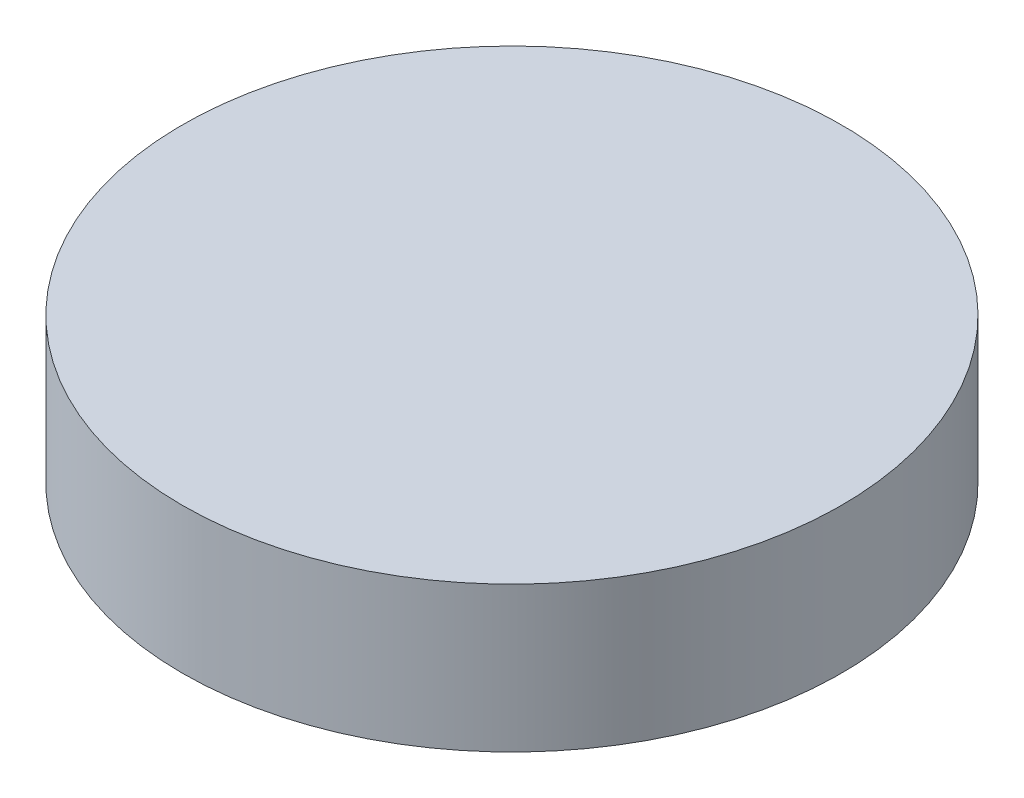
SolidWorks part; units mm, degrees
ref_plane "Front Plane" through (0, 0, 0) normal (0, 0, 1) x (1, 0, 0)
ref_plane "Top Plane" through (0, 0, 0) normal (0, 1, 0) x (1, 0, 0)
ref_plane "Right Plane" through (0, 0, 0) normal (1, 0, 0) x (0, 0, -1)
sketch "Sketch1" plane through (0, 0, 0) normal (0, 1, 0) x (1, 0, 0)
  circle A0 centre (0, 0) radius 34
extrude "Boss-Extrude2" add sketch "Sketch1" along normal blind 15
sketch "Sketch4" plane through (0, 0, 0) normal (0, -1, 0) x (1, 0, 0)
  circle A0 centre (12, 0) radius 3
extrude "Cut-Extrude1" cut sketch "Sketch4" against normal blind 10
